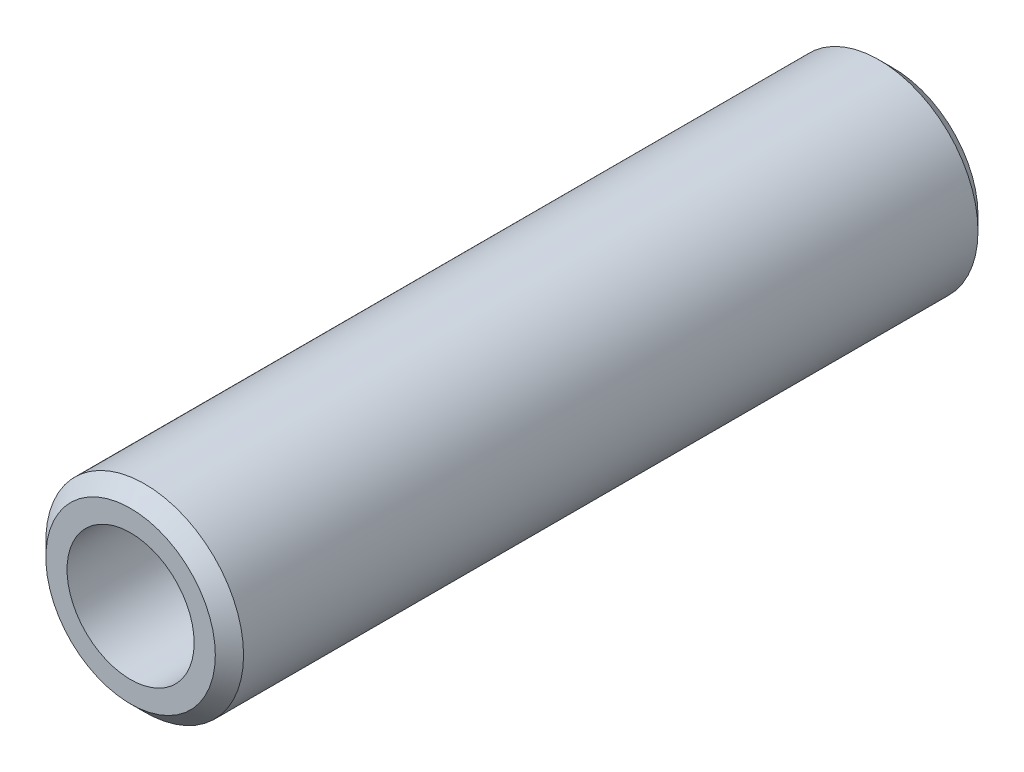
SolidWorks part; units mm, degrees
ref_plane "Plan de face" through (0, 0, 0) normal (0, 0, 1) x (1, 0, 0)
ref_plane "Plan de dessus" through (0, 0, 0) normal (0, 1, 0) x (1, 0, 0)
ref_plane "Plan de droite" through (0, 0, 0) normal (1, 0, 0) x (0, 0, -1)
sketch "Esquisse1" plane through (0, 0, 0) normal (0, 0, 1) x (1, 0, 0)
  circle A0 centre (0, 0) radius 3.5
  circle A1 centre (0, 0) radius 2.25
  dimension "D1" = 7
  dimension "D2" = 4.5
extrude "Boss.-Extru.1" add sketch "Esquisse1" along normal mid plane 27
chamfer "Chanfrein1" distance 0.5 angle 45 2 edges at (3.5, 0, -13.5) (3.5, 0, 13.5)
